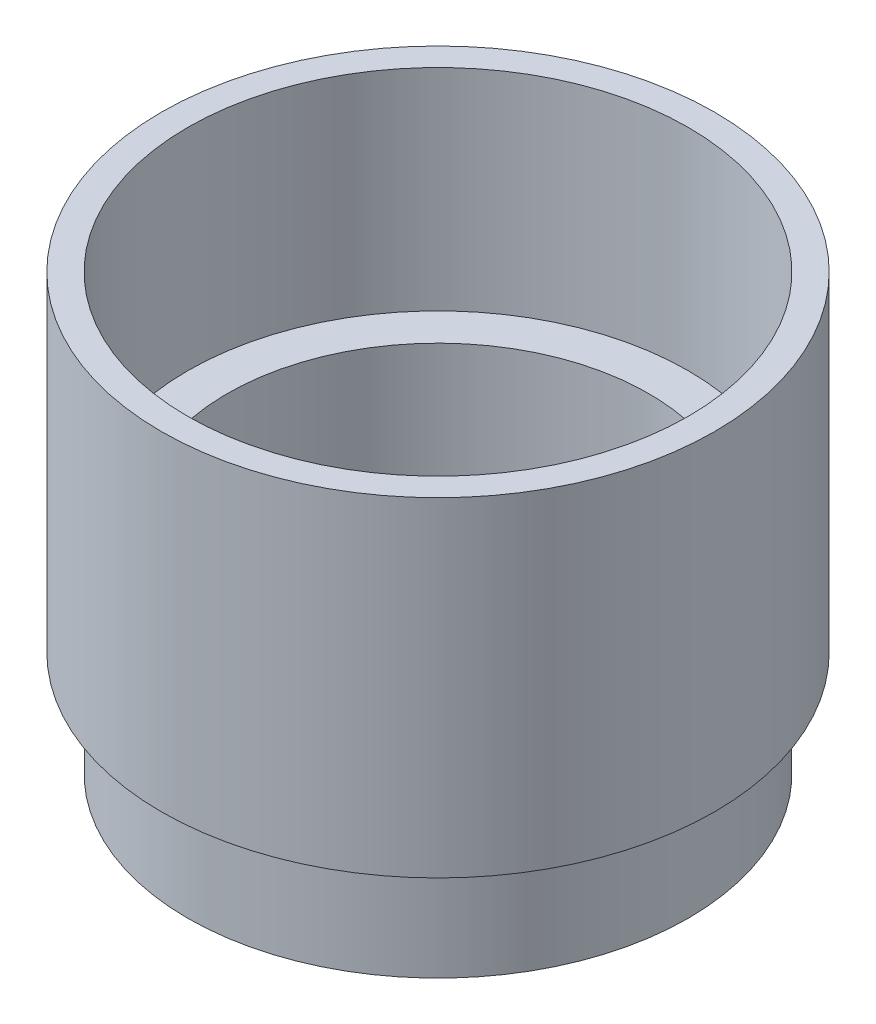
SolidWorks part; units mm, degrees
ref_plane "Front Plane" through (0, 0, 0) normal (0, 0, 1) x (1, 0, 0)
ref_plane "Top Plane" through (0, 0, 0) normal (0, 1, 0) x (1, 0, 0)
ref_plane "Right Plane" through (0, 0, 0) normal (1, 0, 0) x (0, 0, -1)
sketch "Sketch1" plane through (0, 0, 0) normal (0, 0, 1) x (1, 0, 0)
  line L0 (0, 0) -> (25.4, 0)
  line L1 (25.4, 0) -> (25.4, 19.05)
  line L2 (30.1625, 44.45) -> (33.3375, 44.45)
  line L3 (33.3375, 44.45) -> (33.3375, 4.7625)
  line L4 (33.3375, 4.7625) -> (30.1625, 4.7625)
  line L5 (30.1625, 4.7625) -> (30.1625, -7.9375)
  line L6 (30.1625, -7.9375) -> (0, -7.9375)
  line L7 (0, 0) -> (0, -7.9375)
  line L8 (25.4, 19.05) -> (30.1625, 19.05)
  line L9 (30.1625, 19.05) -> (30.1625, 44.45)
  dimension "D1" = 25.4
  dimension "D2" = 33.3375
  dimension "D3" = 30.1625
  dimension "D4" = 12.7
  dimension "D5" = 30.1625
  dimension "D6" = 7.9375
  dimension "D7" = 19.05
  dimension "D8" = 25.4
revolve "Revolve1" add sketch "Sketch1" angle 360 about L7
sketch "Sketch2" plane through (0, 0, 0) normal (0, 1, 0) x (1, 0, 0)
  line L0 (19.05, -9.525) -> (-19.05, 9.525) construction
  line L5 (19.05, 9.525) -> (-19.05, 9.525)
  line L6 (19.05, 9.525) -> (19.05, -9.525)
  line L7 (19.05, -9.525) -> (-19.05, -9.525)
  line L8 (-19.05, 9.525) -> (-19.05, -9.525)
  point P4 (0, 0)
  point P6 (-21.9622, -7.2825)
  dimension "D1" = 19.05
  dimension "D2" = 38.1
extrude "Cut-Extrude1" cut sketch "Sketch2" against normal blind 5.08
fillet "Fillet1" radius 4.7625 4 edges at (-19.05, -2.54, -9.525) (19.05, -2.54, -9.525) (19.05, -2.54, 9.525) (-19.05, -2.54, 9.525)
